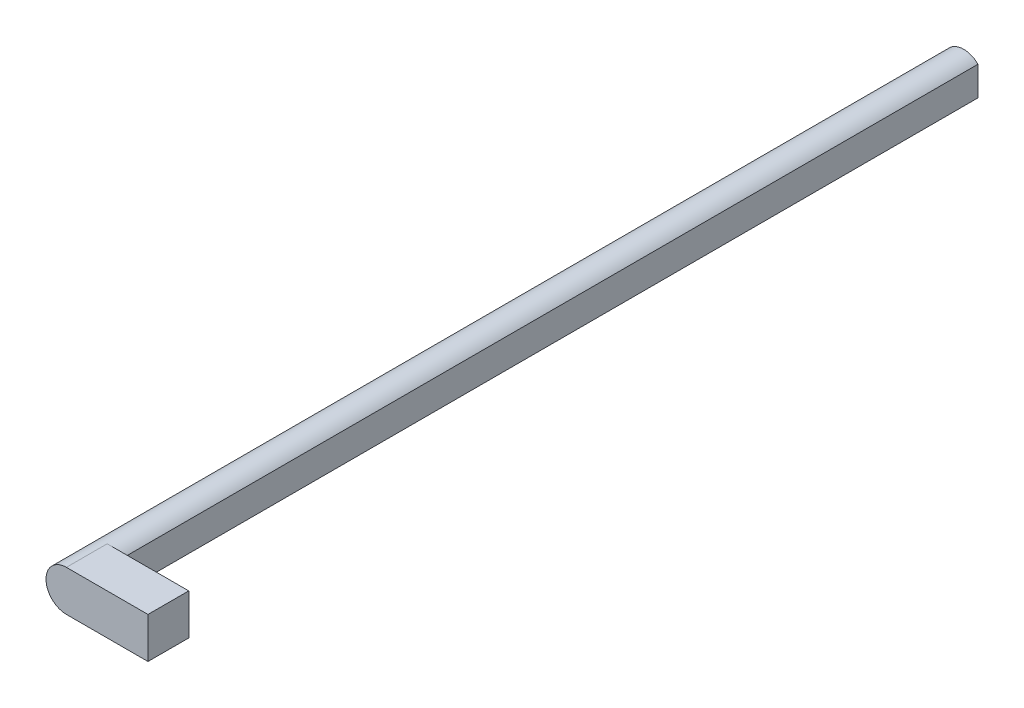
SolidWorks part; units mm, degrees
material "ABS"
ref_plane "Plano frontal" through (0, 0, 0) normal (0, 0, 1) x (1, 0, 0)
ref_plane "Plano superior" through (0, 0, 0) normal (0, 1, 0) x (1, 0, 0)
ref_plane "Plano direito" through (0, 0, 0) normal (1, 0, 0) x (0, 0, -1)
sketch "Esboço1" plane through (0, 0, 0) normal (0, 0, 1) x (1, 0, 0)
  line L0 (-10.1858, 0) -> (9.8467, 0) construction
  line L1 (3.5, -5) -> (6.5, -5)
  line L2 (3.5, -5) -> (3.5, 5)
  line L3 (3.5, 5) -> (6.5, 5)
  line L4 (6.5, -5) -> (6.5, 5)
  line L5 (3.5, -5) -> (6.5, 5) construction
  line L6 (3.5, 5) -> (6.5, -5) construction
  circle A0 centre (0, 0) radius 5
  point P4 (5, 0)
  point P10 (-10.1858, 0)
  point P11 (0, 0)
  point P12 (0, 0)
  dimension "D1" = 10
  dimension "D2" = 10
  dimension "D3" = 3
extrude "Ressalto-extrusão1" add sketch "Esboço1" along normal blind 220 contours L2 A0
sketch "Esboço2" plane through (0, 0, 0) normal (1, 0, 0) x (0, 0, -1)
  line L0 (-234.6068, 0) -> (12.224, 0) construction
  line L1 (-220, 5) -> (-220, -5) construction
  line L2 (-220, -5) -> (-210, -5)
  line L3 (-220, -5) -> (-220, 5)
  line L4 (-220, 5) -> (-210, 5)
  line L5 (-210, -5) -> (-210, 5)
  line L6 (-220, -5) -> (-210, 5) construction
  line L7 (-220, 5) -> (-210, -5) construction
  point P2 (-215, 0)
  point P8 (0, 0)
  dimension "D1" = 10
  dimension "D2" = 10
extrude "Ressalto-extrusão2" add sketch "Esboço2" along normal blind 20
